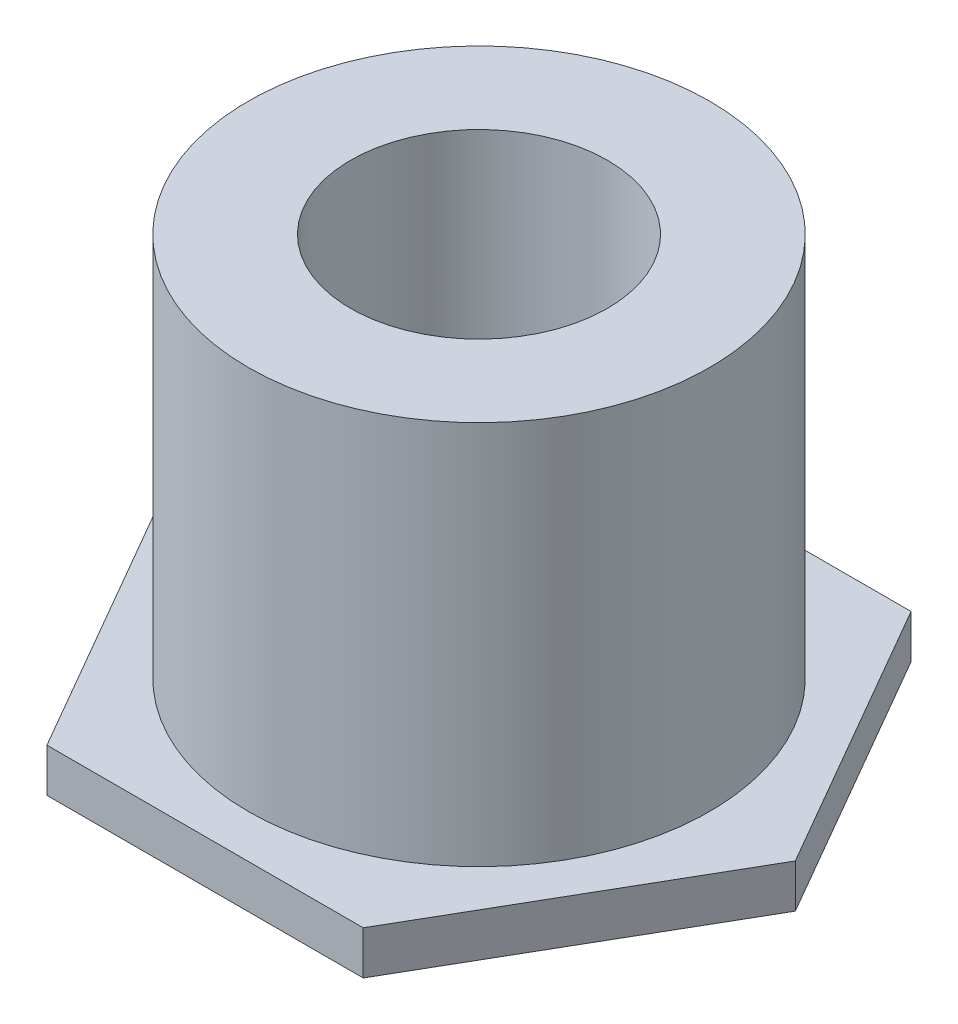
SolidWorks part; units mm, degrees
ref_plane "Front Plane" through (0, 0, 0) normal (0, 0, 1) x (1, 0, 0)
ref_plane "Top Plane" through (0, 0, 0) normal (0, 1, 0) x (1, 0, 0)
ref_plane "Right Plane" through (0, 0, 0) normal (1, 0, 0) x (0, 0, -1)
sketch "Sketch1" plane through (0, 0, 0) normal (0, 1, 0) x (1, 0, 0)
  line L1 (1.8475, -3.2) -> (3.695, 0)
  line L2 (3.695, 0) -> (1.8475, 3.2)
  line L3 (1.8475, 3.2) -> (-1.8475, 3.2)
  line L4 (-1.8475, 3.2) -> (-3.695, 0)
  line L5 (-3.695, 0) -> (-1.8475, -3.2)
  line L6 (-1.8475, -3.2) -> (1.8475, -3.2)
  circle A0 centre (0, 0) radius 3.2 construction
  dimension "D1" = 6.4
extrude "Boss-Extrude1" add sketch "Sketch1" along normal blind 0.508
sketch "Sketch2" plane through (0, 0, 0) normal (0, -1, 0) x (1, 0, 0)
  circle A0 centre (0, 0) radius 2.695
  circle A1 centre (0, 0) radius 1.5
  dimension "D1" = 5.39
  dimension "D2" = 3
extrude "Boss-Extrude2" add sketch "Sketch2" against normal blind 5
